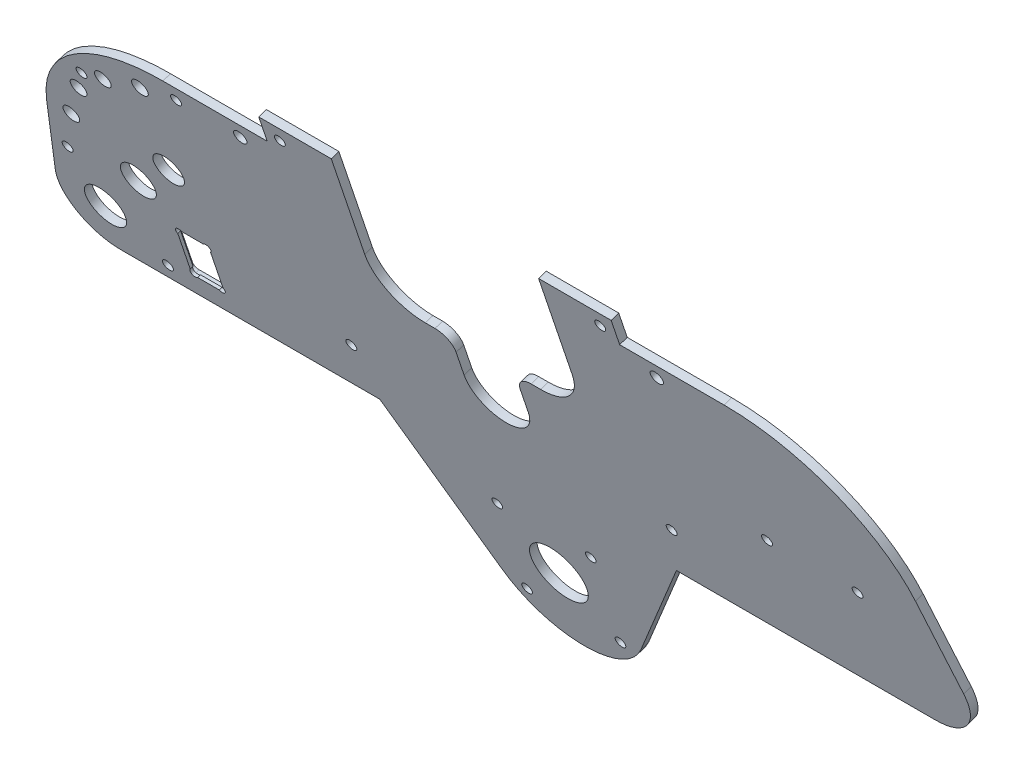
SolidWorks part; units mm, degrees
material "6061-T6 (SS)"
ref_plane "Front" through (0, 0, 0) normal (0, 0, 1) x (1, 0, 0)
ref_plane "Top" through (0, 0, 0) normal (0, 1, 0) x (1, 0, 0)
ref_plane "Right" through (0, 0, 0) normal (1, 0, 0) x (0, 0, -1)
sketch "Sketch1" plane through (0, -336.5004, 1001.0435) normal (0, 0.3186, -0.9479) x (-1, 0, 0)
  line L1 (-58.7894, 930.5791) -> (-27.4963, 876.3779)
  line L3 (27.4963, 876.3779) -> (58.7894, 930.5791)
  line L5 (111.2106, 1035.8684) -> (69.85, 1035.8684)
  line L7 (0, 50) -> (0, -50) construction
  line L10 (69.85, 1035.8684) -> (69.85, 1046.4733)
  line L11 (69.85, 1046.4733) -> (-69.85, 1046.4733)
  line L12 (-69.85, 1035.8684) -> (-69.85, 1046.4733)
  line L13 (0, 1046.4733) -> (0, 1035.8684) construction
  line L14 (-185.1475, 930.5791) -> (-58.7894, 930.5791)
  line L15 (179.0357, 990.6727) -> (227.2983, 772.4975) construction
  line L16 (69.85, 1035.8684) -> (-69.85, 1035.8684) construction
  line L18 (179.0357, 990.6727) -> (227.2983, 772.4975) construction
  line L19 (185.1475, 930.5791) -> (58.7894, 930.5791)
  line L20 (172.1892, 989.1582) -> (185.1475, 930.5791)
  line L21 (58.7894, 930.5791) -> (-58.7894, 930.5791) construction
  line L22 (0, 930.5791) -> (0, 892.2529) construction
  line L23 (172.1892, 989.1582) -> (220.4519, 770.983) construction
  line L24 (-172.1892, 989.1582) -> (-185.1475, 930.5791)
  line L25 (-111.2106, 1035.8684) -> (-69.85, 1035.8684)
  circle A6 centre (0, 892.2529) radius 31.75
  arc A7 (-27.4963, 876.3779) -> (27.4963, 876.3779) centre (0, 892.2529) ccw
  circle A23 centre (0, 892.2529) radius 11.1125
  ellipse E0 centre (111.2106, 977.1923) end of major axis (41.9106, 977.1923) minor radius 65.688 (179.0357, 990.6727) -> (111.2106, 1042.8803) ccw construction
  ellipse E1 centre (111.2106, 977.1923) end of major axis (180.5106, 977.1923) minor radius 65.688 (179.0357, 990.6727) -> (111.2106, 1042.8803) ccw construction
  spline S0 degree 1 poles (172.1892, 989.1582) (111.2106, 1035.8684) knots 0 0 1 1 construction
  spline S1 degree 3 poles (172.1892, 989.1582) (170.7498, 995.6653) (165.5228, 1008.1749) (151.4055, 1023.514) (135.7115, 1031.867) (121.8964, 1035.291) (114.7655, 1035.8684) (111.2106, 1035.8684) knots 0.206687 0.206687 0.206687 0.206687 0.547714 0.888741 1.229769 1.400283 1.570796 1.570796 1.570796 1.570796
  spline S2 degree 3 poles (-172.1892, 989.1582) (-170.7498, 995.6653) (-165.5228, 1008.1749) (-151.4055, 1023.514) (-135.7115, 1031.867) (-121.8964, 1035.291) (-114.7655, 1035.8684) (-111.2106, 1035.8684) knots 0.206687 0.206687 0.206687 0.206687 0.547714 0.888741 1.229769 1.400283 1.570796 1.570796 1.570796 1.570796
  point P12 (0, 892.2529)
  point P26 (-63.5, 1040.1233)
  dimension "D2" = 22.225
  dimension "D1" = 60
  dimension "D3" = 6.35
  dimension "D4" = 6.35
  dimension "D6" = 0
extrude "Boss-Extrude1" add sketch "Sketch1" along normal blind 3.175
hole_wizard "1/4-20 Tapped Hole1" positions "Sketch2" profile "Sketch3" tap size "1/4-20" standard "ANSI Inch" end condition through all
sketch "Sketch2" plane through (0, -335.4888, 998.034) normal (0, 0.3186, -0.9479) x (-1, 0, 0)
  circle A2 centre (-82.55, 1029.5184) radius 2.5527 construction
  circle A3 centre (82.55, 1029.5184) radius 2.5527 construction
  point P0 (82.55, 1029.5184)
  point P2 (-82.55, 1029.5184)
sketch "Sketch3" plane through (-82.55, 640.3705, 1326.0687) normal (1, 0, 0) x (0, 0.9479, 0.3186)
  line L0 (0, 0) -> (0, 59.3422)
  line L1 (0, 59.3422) -> (2.5527, 59.3422)
  line L2 (2.5527, 59.3422) -> (2.5527, 0)
  line L5 (2.5527, 0) -> (0, 0)
  line L11 (0, -6.35) -> (0, 107.95) construction
  dimension "Thru Tap Drill Dia." = 5.1054
  dimension "Thru Tap Drill Depth" = 59.3422
cosmetic thread "Hole Thread1" parameters "D1"=3.175, "D2"=6.35
cosmetic thread "Hole Thread2" parameters "D1"=3.175, "D2"=6.35
hole_wizard "#10-32 Tapped Hole1" positions "Sketch4" profile "Sketch5" tap size "#10-32" standard "ANSI Inch" end condition through all
sketch "Sketch4" plane through (0, -335.4888, 998.034) normal (0, 0.3186, -0.9479) x (-1, 0, 0)
  point P21 (-18.5218, 873.7311)
  point P23 (18.5218, 873.7311)
  point P25 (18.5218, 910.7747)
  point P27 (-18.5218, 910.7747)
sketch "Sketch5" plane through (18.5218, 492.7029, 1276.4304) normal (1, 0, 0) x (0, 0.9479, 0.3186)
  line L0 (0, 0) -> (0, 59.3422)
  line L1 (0, 59.3422) -> (2.0193, 59.3422)
  line L2 (2.0193, 59.3422) -> (2.0193, 0)
  line L5 (2.0193, 0) -> (0, 0)
  line L11 (0, -6.35) -> (0, 107.95) construction
  dimension "Thru Tap Drill Dia." = 4.0386
  dimension "Thru Tap Drill Depth" = 59.3422
cosmetic thread "Hole Thread3" parameters "D1"=3.175, "D2"=4.826
cosmetic thread "Hole Thread4" parameters "D1"=3.175, "D2"=4.826
cosmetic thread "Hole Thread5" parameters "D1"=3.175, "D2"=4.826
cosmetic thread "Hole Thread6" parameters "D1"=3.175, "D2"=4.826
hole_wizard "#8-32 Tapped Hole1" positions "Sketch6" profile "Sketch7" tap size "#8-32" standard "ANSI Inch" end condition through all
sketch "Sketch6" plane through (0, -336.5004, 1001.0435) normal (0, -0.3186, 0.9479) x (1, 0, 0)
  point P10 (63.5, 1040.1233)
  point P13 (63.5, 951.2233)
  point P16 (-63.5, 951.2233)
  point P19 (-63.5, 1040.1233)
sketch "Sketch7" plane through (63.5, 649.411, 1332.4573) normal (1, 0, 0) x (0, -0.9479, -0.3186)
  line L0 (0, 0) -> (0, 59.3422)
  line L1 (0, 59.3422) -> (2.0828, 59.3422)
  line L2 (2.0828, 59.3422) -> (2.0828, 0)
  line L5 (2.0828, 0) -> (0, 0)
  line L11 (0, -6.35) -> (0, 107.95) construction
  dimension "Thread Major Dia." = 4.1656
  dimension "Thru Tap Drill Depth" = 59.3422
sketch "Sketch8" plane through (0, -335.4888, 998.034) normal (0, 0.3186, -0.9479) x (-1, 0, 0)
  line L0 (-41.0905, 1028.9473) -> (-41.0905, 1004.8173) construction
  line L1 (-22.86, 986.5868) -> (22.86, 986.5868) construction
  line L2 (41.0905, 1004.8173) -> (41.0905, 1028.9473) construction
  line L3 (69.85, 1046.4733) -> (-69.85, 1046.4733) construction
  line L4 (-41.0905, 1046.4733) -> (-41.0905, 1004.8173)
  line L5 (-22.86, 986.5868) -> (-19.05, 986.5868)
  line L6 (41.0905, 1004.8173) -> (41.0905, 1046.4733)
  line L8 (12.7, 970.2733) -> (12.7, 980.2368)
  line L9 (41.0905, 1046.4733) -> (-41.0905, 1046.4733)
  line L11 (-12.7, 970.2733) -> (-12.7, 980.2368)
  line L12 (19.05, 986.5868) -> (22.86, 986.5868)
  arc A1 (-12.7, 970.2733) -> (12.7, 970.2733) centre (0, 970.2733) ccw
  arc A3 (12.7, 980.2368) -> (19.05, 986.5868) centre (19.05, 980.2368) cw
  arc A4 (-12.7, 980.2368) -> (-19.05, 986.5868) centre (-19.05, 980.2368) ccw
  arc A5 (41.0905, 1004.8173) -> (22.86, 986.5868) centre (22.86, 1004.8173) cw
  arc A6 (-22.86, 986.5868) -> (-41.0905, 1004.8173) centre (-22.86, 1004.8173) cw
  point P16 (12.7, 986.5868)
  dimension "D1" = 25.4
  dimension "D2" = 6.35
extrude "Cut-Extrude1" cut sketch "Sketch8" against normal through all
fillet "Fillet1" radius 19.05 2 edges at (-185.1475, 546.0822, 1296.0486) (185.1475, 546.0822, 1296.0486)
hole_wizard "#8-32 Tapped Hole2" positions "Sketch10" profile "Sketch11" tap size "#8-32" standard "ANSI Inch" end condition through all
sketch "Sketch10" plane through (0, -335.4888, 998.034) normal (0, 0.3186, -0.9479) x (-1, 0, 0)
  point P1 (140.7347, 936.9291)
  point P3 (169.9061, 970.0794)
  point P5 (150.1977, 1014.7054)
  point P7 (107.9928, 1029.5184)
sketch "Sketch11" plane through (-140.7347, 552.607, 1296.5671) normal (1, 0, 0) x (0, 0.9479, 0.3186)
  line L0 (0, 0) -> (0, 59.3422)
  line L1 (0, 59.3422) -> (2.0828, 59.3422)
  line L2 (2.0828, 59.3422) -> (2.0828, 0)
  line L5 (2.0828, 0) -> (0, 0)
  line L11 (0, -6.35) -> (0, 107.95) construction
  dimension "Thread Major Dia." = 4.1656
  dimension "Thru Tap Drill Depth" = 59.3422
hole_wizard "#10-32 Tapped Hole2" positions "Sketch12" profile "Sketch13" tap size "#8-32" standard "ANSI Inch" end condition through all
sketch "Sketch12" plane through (0, -335.4888, 998.034) normal (0, 0.3186, -0.9479) x (-1, 0, 0)
  point P12 (-109.05, 975.5791)
  point P14 (-144.95, 975.5791)
sketch "Sketch13" plane through (109.05, 589.2426, 1308.8821) normal (1, 0, 0) x (0, 0.9479, 0.3186)
  line L0 (0, 0) -> (0, 59.3422)
  line L1 (0, 59.3422) -> (2.0828, 59.3422)
  line L2 (2.0828, 59.3422) -> (2.0828, 0)
  line L5 (2.0828, 0) -> (0, 0)
  line L11 (0, -6.35) -> (0, 107.95) construction
  dimension "Thread Major Dia." = 4.1656
  dimension "Thru Tap Drill Depth" = 59.3422
sketch "Sketch14" plane through (0, -335.4888, 998.034) normal (0, 0.3186, -0.9479) x (-1, 0, 0)
  line L0 (117.3097, 957.0577) -> (117.3097, 942.2006) construction
  line L1 (126.3097, 939.6291) -> (121.3097, 939.6291) construction
  line L2 (130.3097, 942.2006) -> (130.3097, 957.0577) construction
  line L3 (121.3097, 959.6291) -> (126.3097, 959.6291) construction
  line L4 (117.3097, 959.6291) -> (117.3097, 939.6291)
  line L5 (130.3097, 939.6291) -> (117.3097, 939.6291)
  line L6 (130.3097, 939.6291) -> (130.3097, 959.6291)
  line L7 (117.3097, 959.6291) -> (130.3097, 959.6291)
  circle A0 centre (123.8097, 1024.9202) radius 3.175 construction
  circle A1 centre (123.8097, 1024.9202) radius 3.175
  circle A2 centre (140.7347, 1017.9182) radius 3.175 construction
  circle A3 centre (140.7347, 1017.9182) radius 3.175
  circle A4 centre (154.2721, 1005.5802) radius 3.175 construction
  circle A5 centre (154.2721, 1005.5802) radius 3.175
  circle A6 centre (162.384, 989.1582) radius 3.175 construction
  circle A7 centre (162.384, 989.1582) radius 3.175
  circle A8 centre (161.4229, 949.6291) radius 8 construction
  circle A9 centre (161.4229, 949.6291) radius 8
  arc A10 (145.0268, 968.4494) -> (136.4427, 968.4494) centre (140.7347, 973.7326) ccw construction
  arc A11 (145.0268, 968.4494) -> (136.4427, 968.4494) centre (140.7347, 973.7326) ccw
  arc A12 (126.7795, 983.9512) -> (120.8398, 983.9512) centre (123.8097, 989.1582) ccw construction
  arc A13 (126.7795, 983.9512) -> (120.8398, 983.9512) centre (123.8097, 989.1582) ccw
  arc A14 (126.7795, 983.9512) -> (120.8398, 983.9512) centre (123.8097, 989.1582) cw
  arc A15 (136.4427, 968.4494) -> (145.0268, 968.4494) centre (140.7347, 973.7326) ccw
extrude "Cut-Extrude2" cut sketch "Sketch14" against normal through all and the other way through all
sketch "Sketch15" plane through (0, -335.4888, 998.034) normal (0, 0.3186, -0.9479) x (-1, 0, 0)
  line L4 (131.0597, 962.4506) -> (116.5597, 962.4506)
  line L5 (114.5597, 960.4506) -> (114.5597, 939.9506)
  line L6 (116.5597, 937.9506) -> (131.0597, 937.9506)
  line L7 (133.0597, 939.9506) -> (133.0597, 960.4506)
  line L8 (131.0597, 962.4506) -> (116.5597, 962.4506)
  line L9 (114.5597, 960.4506) -> (114.5597, 939.9506)
  line L10 (116.5597, 937.9506) -> (131.0597, 937.9506)
  line L11 (133.0597, 939.9506) -> (133.0597, 960.4506)
  arc A4 (116.5597, 962.4506) -> (114.5597, 960.4506) centre (116.5597, 960.4506) ccw
  arc A5 (114.5597, 939.9506) -> (116.5597, 937.9506) centre (116.5597, 939.9506) ccw
  arc A6 (131.0597, 937.9506) -> (133.0597, 939.9506) centre (131.0597, 939.9506) ccw
  arc A7 (133.0597, 960.4506) -> (131.0597, 962.4506) centre (131.0597, 960.4506) ccw
  arc A8 (116.5597, 962.4506) -> (114.5597, 960.4506) centre (116.5597, 960.4506) ccw
  arc A9 (114.5597, 939.9506) -> (116.5597, 937.9506) centre (116.5597, 939.9506) ccw
  arc A10 (131.0597, 937.9506) -> (133.0597, 939.9506) centre (131.0597, 939.9506) ccw
  arc A11 (133.0597, 960.4506) -> (131.0597, 962.4506) centre (131.0597, 960.4506) ccw
  dimension "D1" = 0
extrude "Cut-Extrude3" cut sketch "Sketch15" against normal up to surface (2 mm away)
sketch "Sketch16" plane through (0, -336.1261, 999.9297) normal (0, 0.3186, -0.9479) x (-1, 0, 0)
  line L0 (117.3097, 959.6291) -> (118.4322, 958.5066) construction
  line L1 (129.1871, 958.5066) -> (130.3097, 959.6291) construction
  line L2 (129.1871, 940.7517) -> (130.3097, 939.6291) construction
  line L3 (117.3097, 939.6291) -> (118.4322, 940.7517) construction
  line L4 (117.3097, 939.6291) -> (130.3097, 939.6291) construction
  line L5 (130.3097, 959.6291) -> (117.3097, 959.6291) construction
  circle A0 centre (118.4322, 958.5066) radius 1.5875
  circle A1 centre (129.1871, 958.5066) radius 1.5875
  circle A2 centre (129.1871, 940.7517) radius 1.5875
  circle A3 centre (118.4322, 940.7517) radius 1.5875
  dimension "D1" = 3.175
  dimension "D2" = 3.175
  dimension "D3" = 3.175
  dimension "D4" = 3.175
  dimension "D5" = 45
  dimension "D6" = 45
  dimension "D7" = 45
  dimension "D8" = 45
extrude "Cut-Extrude4" cut sketch "Sketch16" against normal through all
